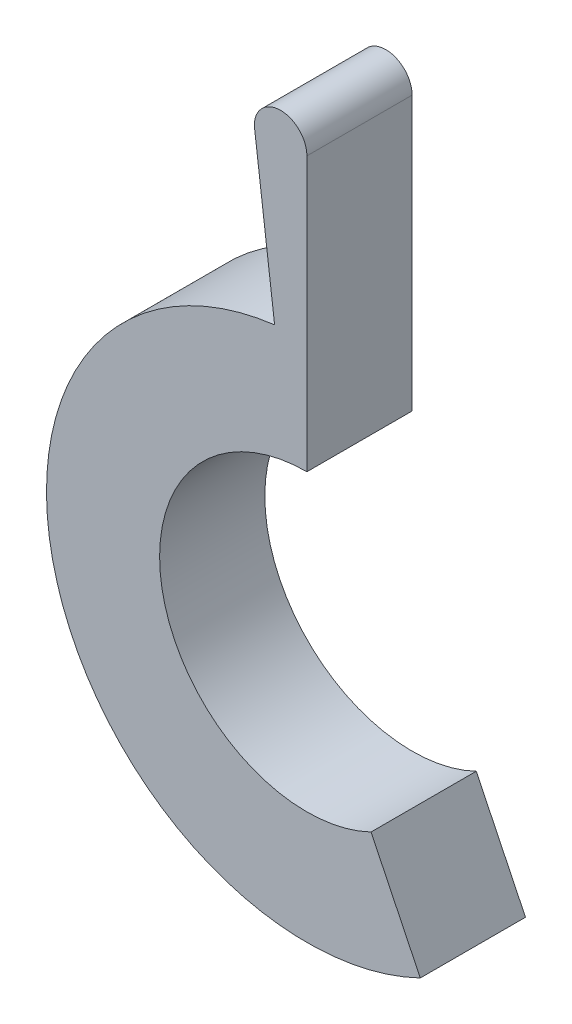
SolidWorks part; units mm, degrees
ref_plane "Plano frontal" through (0, 0, 0) normal (0, 0, 1) x (1, 0, 0)
ref_plane "Plano superior" through (0, 0, 0) normal (0, 1, 0) x (1, 0, 0)
ref_plane "Plano direito" through (0, 0, 0) normal (1, 0, 0) x (0, 0, -1)
sketch "Esboço1" plane through (0, 0, 0) normal (0, 0, 1) x (1, 0, 0)
  line L0 (0, 0) -> (10, 0) construction
  line L1 (0, 0) -> (-10, 0) construction
  line L2 (-10, 0) -> (-10, -9.798) construction
  line L6 (0, 20) -> (0, 40)
  line L7 (-5, 40) -> (-3.0699, 24.5589)
  line L8 (6.0951, -12.6035) -> (10.7753, -22.2813)
  line L9 (0, 20) -> (0, 14)
  arc A2 (0, 24.75) -> (-3.0699, 24.5589) centre (0, 0) ccw construction
  arc A3 (0, 40) -> (-4.9231, 39.3846) centre (-2.5, 40) ccw
  arc A4 (-3.0699, 24.5589) -> (10.7753, -22.2813) centre (0, 0) ccw
  arc A5 (0, 14) -> (6.0951, -12.6035) centre (0, 0) ccw
  dimension "D1" = 49.5
  dimension "D2" = 20
  dimension "D3" = 10
  dimension "D4" = 5
extrude "Ressalto-extrusão1" add sketch "Esboço1" along normal blind 10
